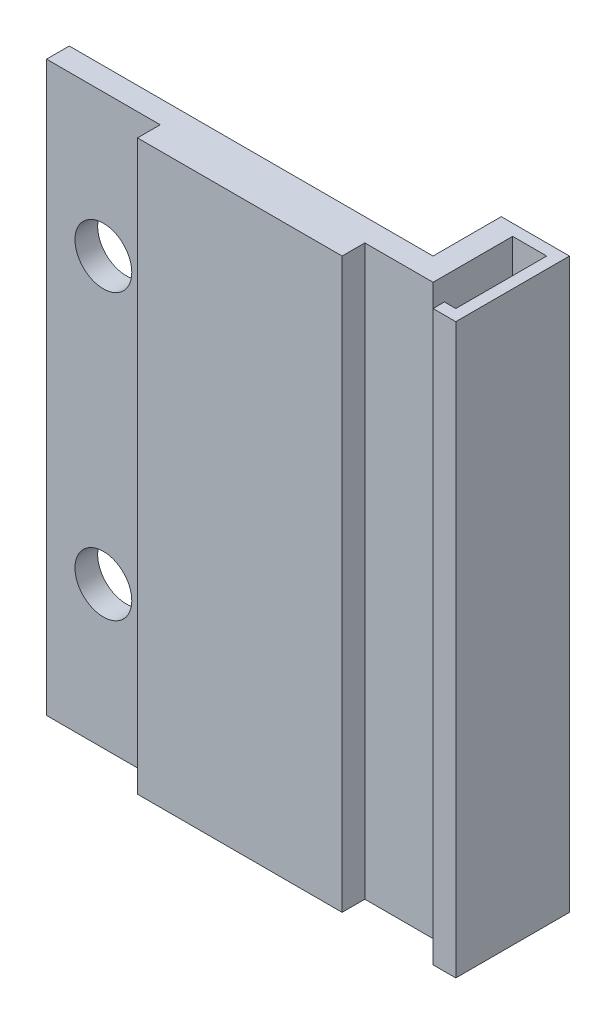
SolidWorks part; units mm, degrees
material "ABS"
ref_plane "Plan de face" through (0, 0, 0) normal (0, 0, 1) x (1, 0, 0)
ref_plane "Plan de dessus" through (0, 0, 0) normal (0, 1, 0) x (1, 0, 0)
ref_plane "Plan de droite" through (0, 0, 0) normal (1, 0, 0) x (0, 0, -1)
sketch "Esquisse1" plane through (0, 0, 0) normal (0, 0, 1) x (1, 0, 0)
  line L0 (5, 50) -> (5, 0) construction
  line L1 (0, 0) -> (12, 0)
  line L2 (0, 0) -> (0, 50)
  line L3 (0, 50) -> (12, 50)
  line L4 (12, 0) -> (12, 50)
  line L5 (0, 50) -> (10, 50)
  line L6 (0, 50) -> (0, 0)
  line L7 (0, 0) -> (10, 0)
  line L8 (10, 50) -> (10, 0)
  circle A0 centre (5, 37.5) radius 2.5
  circle A1 centre (5, 12.5) radius 2.5
  dimension "D5" = 5
  dimension "D6" = 5
  dimension "D1" = 12
  dimension "D2" = 50
  dimension "D3" = 2
  dimension "D4" = 5
  dimension "D7" = 12.5
  dimension "D8" = 12.5
extrude "Boss.-Extru.1" add sketch "Esquisse1" along normal blind 2 contours L5 L0 A0 A1 L7 L8 | L0 L3 L2 L1 A1 A0 | L3 L8 L1 L4
sketch "Esquisse2" plane through (0, 0, 2) normal (0, 0, 1) x (1, 0, 0)
  line L0 (0, 0) -> (12, 0) construction
  line L1 (12, 50) -> (10, 50)
  line L2 (12, 50) -> (12, 0)
  line L3 (12, 0) -> (10, 0)
  line L4 (10, 50) -> (10, 0)
  dimension "D1" = 2
extrude "Boss.-Extru.2" add sketch "Esquisse2" along normal blind 2
sketch "Esquisse3" plane through (12, 0, 0) normal (1, 0, 0) x (0, 0, -1)
  line L1 (-4, 50) -> (0, 50)
  line L2 (-4, 50) -> (-4, 0)
  line L3 (-4, 0) -> (0, 0)
  line L4 (0, 50) -> (0, 0)
extrude "Boss.-Extru.3" add sketch "Esquisse3" along normal blind 22
sketch "Esquisse4" plane through (0, 0, 0) normal (0, 0, -1) x (-1, 0, 0)
  line L0 (0, 0) -> (-34, 0) construction
  line L1 (-34, 50) -> (-32, 50)
  line L2 (-34, 50) -> (-34, 0)
  line L3 (-34, 0) -> (-32, 0)
  line L4 (-32, 50) -> (-32, 0)
  dimension "D1" = 2
extrude "Boss.-Extru.4" add sketch "Esquisse4" along normal blind 6
sketch "Esquisse5" plane through (34, 0, 0) normal (1, 0, 0) x (0, 0, -1)
  line L1 (-4, 50) -> (-2, 50)
  line L2 (-4, 50) -> (-4, 0)
  line L3 (-4, 0) -> (-2, 0)
  line L4 (-2, 50) -> (-2, 0)
extrude "Enlèv. mat.-Extru.1" cut sketch "Esquisse5" against normal blind 6
sketch "Esquisse6" plane through (34, 0, 0) normal (1, 0, 0) x (0, 0, -1)
  line L0 (-2, 0) -> (6, 0) construction
  line L1 (6, 50) -> (5, 50)
  line L2 (6, 50) -> (6, 0)
  line L3 (6, 0) -> (5, 0)
  line L4 (5, 50) -> (5, 0)
  dimension "D1" = 1
extrude "Boss.-Extru.5" add sketch "Esquisse6" along normal blind 4
sketch "Esquisse7" plane through (0, 0, -5) normal (0, 0, 1) x (1, 0, 0)
  line L0 (38, 0) -> (34, 0) construction
  line L1 (38, 50) -> (37, 50)
  line L2 (38, 50) -> (38, 0)
  line L3 (38, 0) -> (37, 0)
  line L4 (37, 50) -> (37, 0)
  dimension "D1" = 1
extrude "Boss.-Extru.6" add sketch "Esquisse7" along normal blind 9
sketch "Esquisse8" plane through (37, 0, 0) normal (-1, 0, 0) x (0, 0, 1)
  line L0 (4, 0) -> (-5, 0) construction
  line L1 (4, 50) -> (3, 50)
  line L2 (4, 50) -> (4, 0)
  line L3 (4, 0) -> (3, 0)
  line L4 (3, 50) -> (3, 0)
  dimension "D1" = 1
extrude "Boss.-Extru.7" add sketch "Esquisse8" along normal blind 1
